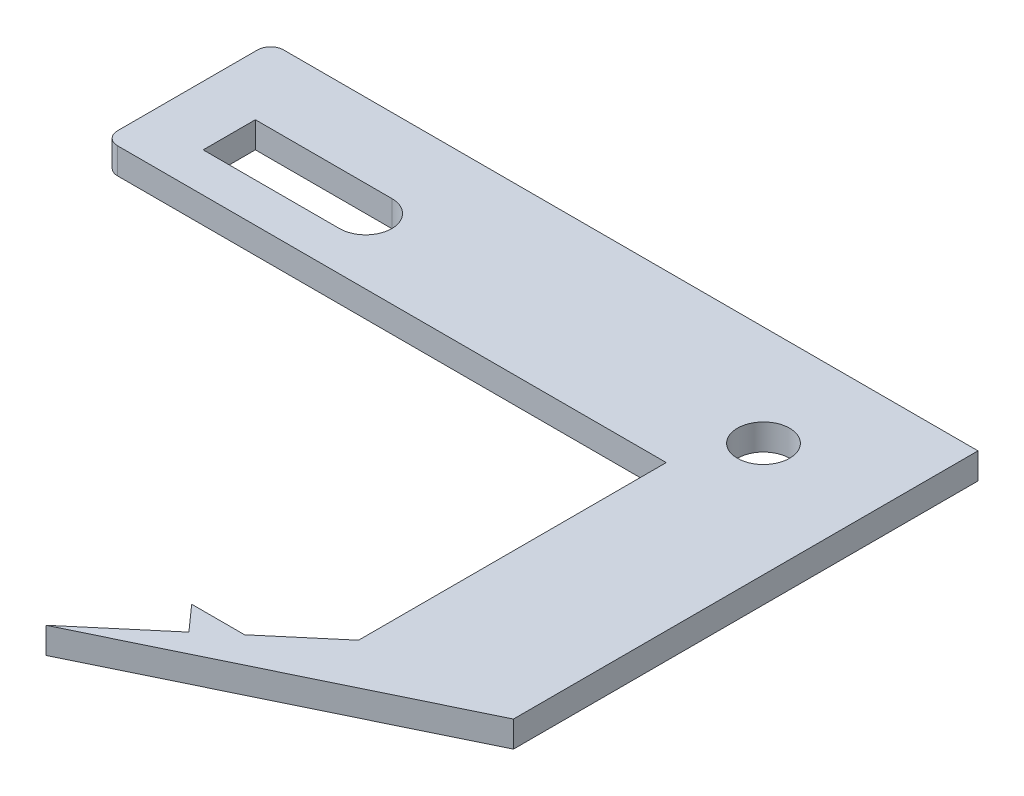
SolidWorks part; units mm, degrees
ref_plane "Front Plane" through (0, 0, 0) normal (0, 0, 1) x (1, 0, 0)
ref_plane "Top Plane" through (0, 0, 0) normal (0, 1, 0) x (1, 0, 0)
ref_plane "Right Plane" through (0, 0, 0) normal (1, 0, 0) x (0, 0, -1)
sketch "Sketch1" plane through (0, 0, 0) normal (0, 1, 0) x (1, 0, 0)
  line L0 (0, 48.4129) -> (0, 37.692)
  line L1 (1, 36.692) -> (31.48, 36.692)
  line L2 (15, 41.7006) -> (15, -27.2696) construction
  line L3 (31.48, 36.692) -> (43.0365, 36.692)
  line L4 (43.0365, 36.692) -> (43.0365, 25.987)
  line L5 (54.2008, 13.8216) -> (54.2008, 36.692)
  line L6 (1, 49.4129) -> (41.48, 49.4129)
  line L7 (41.48, 49.4129) -> (54.2008, 49.4129)
  line L8 (43.0365, 17.1322) -> (43.0365, 25.987)
  line L9 (15, 43.7006) -> (4.5495, 43.7006)
  line L10 (4.5495, 43.7006) -> (4.5495, 39.7006)
  line L11 (4.5495, 39.7006) -> (15, 39.7006)
  line L13 (30.0717, 2.1362) -> (36, 7.1571)
  line L14 (43.0365, 17.1322) -> (43.0365, 13.1165)
  line L15 (54.2008, 49.4129) -> (54.2008, 36.692)
  line L17 (38.3103, 9.1137) -> (43.0365, 13.1165)
  line L19 (36, 7.1571) -> (34.2536, 9.1137)
  line L20 (30.0717, 2.1362) -> (54.2008, 13.8216)
  line L21 (34.2536, 9.1137) -> (38.3103, 9.1137)
  arc A4 (1, 36.692) -> (0, 37.692) centre (1, 37.692) cw
  arc A5 (1, 49.4129) -> (0, 48.4129) centre (1, 48.4129) ccw
  arc A6 (15, 39.7006) -> (15, 43.7006) centre (15, 41.7006) ccw
  circle A7 centre (45.48, 41.7006) radius 2
  point P9 (36, 36.692)
  point P18 (0, 36.692)
  point P21 (0, 49.4129)
  dimension "D5" = 40.48
  dimension "D7" = 1
  dimension "D8" = 15
  dimension "D10" = 4
  dimension "D11" = 30.48
extrude "Boss-Extrude2" add sketch "Sketch1" along normal blind 2
